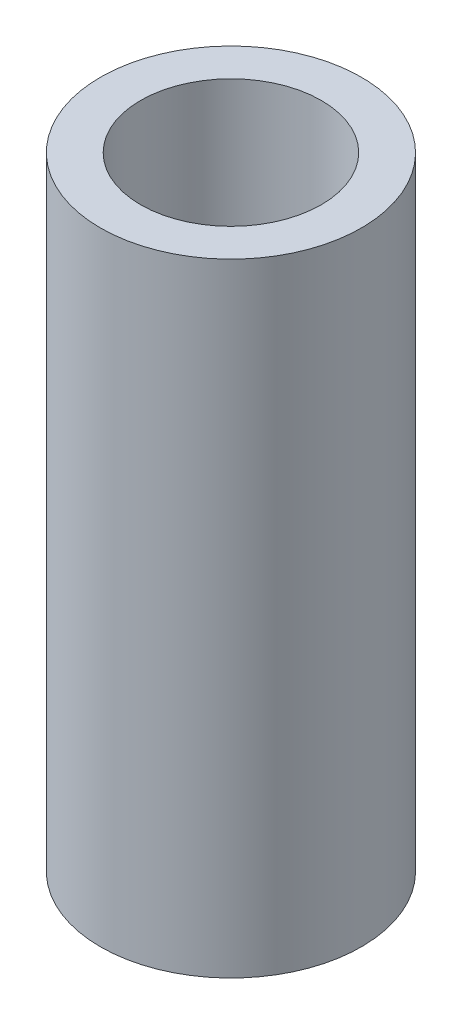
SolidWorks part; units mm, degrees
ref_plane "Front Plane" through (0, 0, 0) normal (0, 0, 1) x (1, 0, 0)
ref_plane "Top Plane" through (0, 0, 0) normal (0, 1, 0) x (1, 0, 0)
ref_plane "Right Plane" through (0, 0, 0) normal (1, 0, 0) x (0, 0, -1)
sketch "Sketch1" plane through (0, 0, 0) normal (0, 1, 0) x (1, 0, 0)
  circle A0 centre (0, 0) radius 3.25
  circle A1 centre (0, 0) radius 2.25
  dimension "D1" = 6.5
  dimension "D2" = 4.5
extrude "Boss-Extrude1" add sketch "Sketch1" along normal blind 15.5
